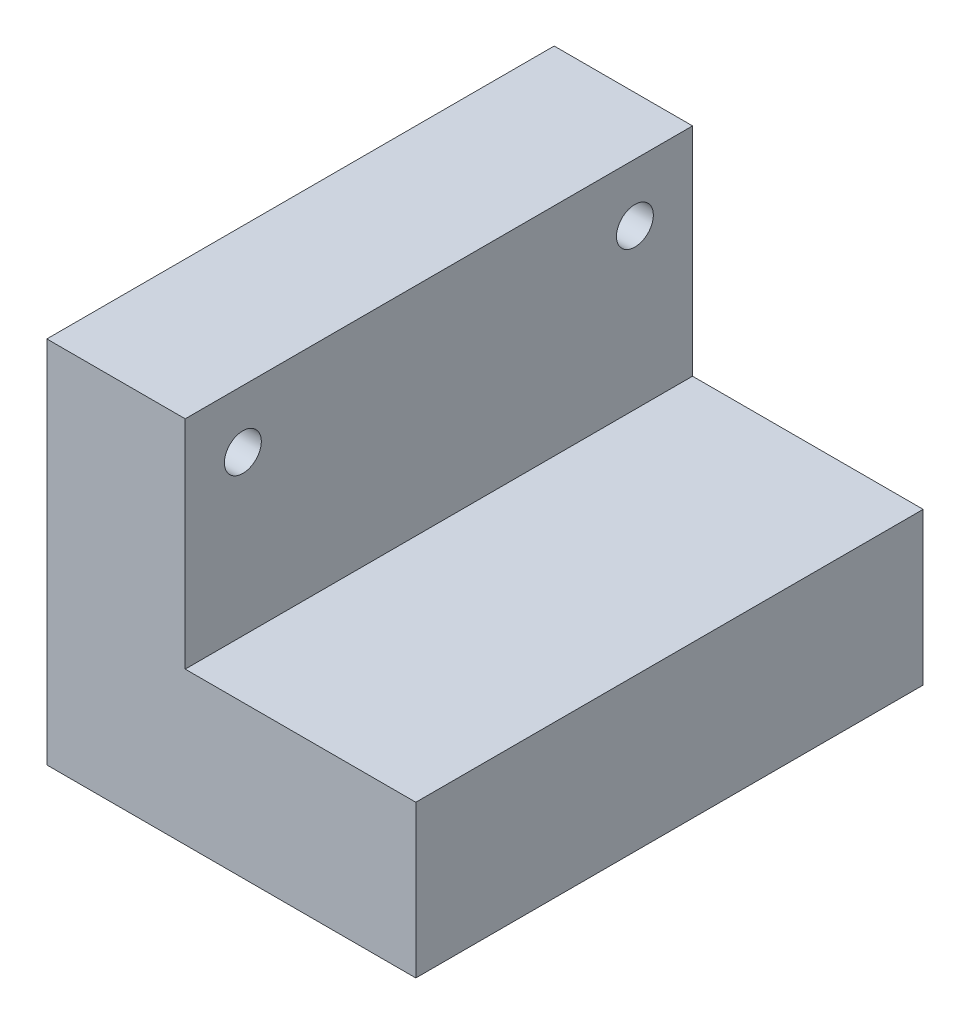
SolidWorks part; units mm, degrees
ref_plane "Front Plane" through (0, 0, 0) normal (0, 0, 1) x (1, 0, 0)
ref_plane "Top Plane" through (0, 0, 0) normal (0, 1, 0) x (1, 0, 0)
ref_plane "Right Plane" through (0, 0, 0) normal (1, 0, 0) x (0, 0, -1)
sketch "Sketch1" plane through (0, 0, 0) normal (0, 1, 0) x (1, 0, 0)
  line L1 (-29.0441, 55.6066) -> (50.9559, 55.6066)
  line L2 (-29.0441, 55.6066) -> (-29.0441, -54.3934)
  line L3 (-29.0441, -54.3934) -> (50.9559, -54.3934)
  line L4 (50.9559, 55.6066) -> (50.9559, -54.3934)
  dimension "D1" = 110
  dimension "D2" = 80
extrude "Boss-Extrude1" add sketch "Sketch1" along normal blind 80
sketch "Sketch2" plane through (0, 80, 0) normal (0, 1, 0) x (1, 0, 0)
  line L0 (-29.0441, -54.3934) -> (50.9559, -54.3934) construction
  line L1 (50.9559, 55.6066) -> (0.9559, 55.6066)
  line L2 (50.9559, 55.6066) -> (50.9559, -54.3934)
  line L3 (50.9559, -54.3934) -> (0.9559, -54.3934)
  line L4 (0.9559, 55.6066) -> (0.9559, -54.3934)
  dimension "D1" = 50
extrude "Cut-Extrude2" cut sketch "Sketch2" against normal blind 47
sketch "Sketch3" plane through (-29.0441, 0, 0) normal (-1, 0, 0) x (0, 0, 1)
  line L0 (54.3934, 80) -> (54.3934, 0) construction
  line L1 (-55.6066, 80) -> (54.3934, 80) construction
  line L2 (-55.6066, 80) -> (-55.6066, 0) construction
  circle A0 centre (41.8934, 67.5) radius 4
  circle A1 centre (-43.1066, 67.5) radius 4
  dimension "D3" = 8
  dimension "D6" = 8
  dimension "D1" = 12.5
  dimension "D2" = 12.5
  dimension "D4" = 12.5
  dimension "D5" = 12.5
extrude "Cut-Extrude3" cut sketch "Sketch3" against normal through all
